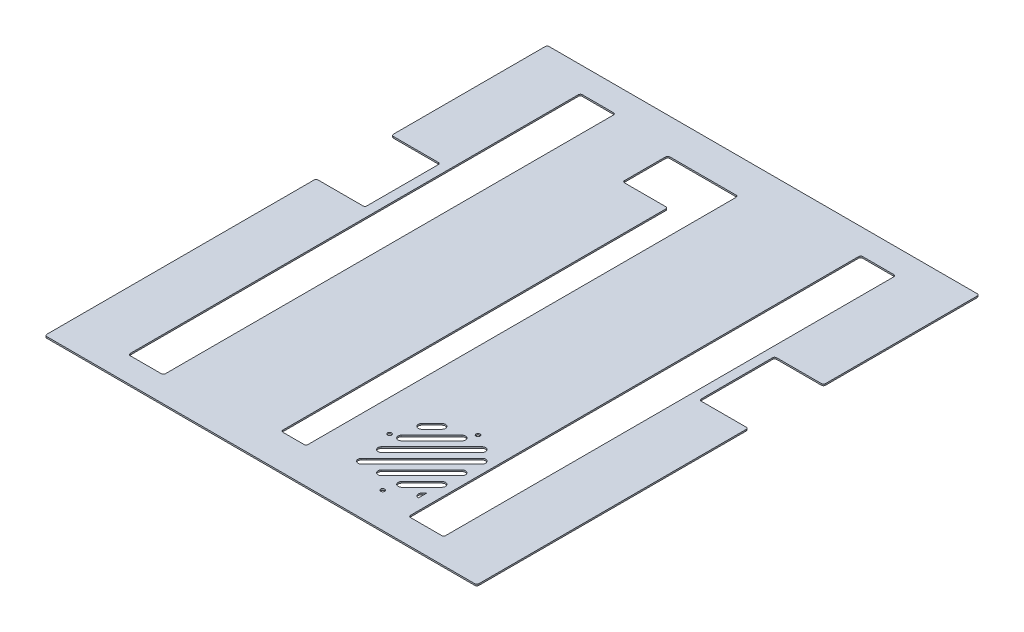
SolidWorks part; units mm, degrees
ref_plane "Front Plane" through (0, 0, 0) normal (0, 0, 1) x (1, 0, 0)
ref_plane "Top Plane" through (0, 0, 0) normal (0, 1, 0) x (1, 0, 0)
ref_plane "Right Plane" through (0, 0, 0) normal (1, 0, 0) x (0, 0, -1)
sketch "Sketch1" plane through (0, 0, 0) normal (0, 1, 0) x (1, 0, 0)
  line L1 (5911.0841, -8452.3124) -> (6341.0841, -8452.3124)
  line L2 (5911.0841, -8452.3124) -> (5911.0841, -8952.3124)
  line L3 (5911.0841, -8952.3124) -> (6341.0841, -8952.3124)
  line L4 (6341.0841, -8452.3124) -> (6341.0841, -8952.3124)
  dimension "D1" = 500
  dimension "D2" = 430
extrude "Boss-Extrude1" add sketch "Sketch1" along normal blind 1.5
sketch "Sketch2" plane through (0, 1.5, 0) normal (0, 1, 0) x (1, 0, 0)
  line L0 (5911.0841, -8452.3124) -> (5911.0841, -8952.3124) construction
  line L1 (5959.6841, -8682.3124) -> (5911.0841, -8682.3124)
  line L2 (5959.6841, -8682.3124) -> (5959.6841, -8607.3124)
  line L3 (5959.6841, -8607.3124) -> (5911.0841, -8607.3124)
  line L4 (5911.0841, -8682.3124) -> (5911.0841, -8607.3124)
  line L9 (6341.0841, -8952.3124) -> (6341.0841, -8452.3124) construction
  line L10 (6341.0841, -8682.3124) -> (6292.4841, -8682.3124)
  line L11 (6341.0841, -8682.3124) -> (6341.0841, -8607.3124)
  line L12 (6341.0841, -8607.3124) -> (6292.4841, -8607.3124)
  line L13 (6292.4841, -8682.3124) -> (6292.4841, -8607.3124)
  line L14 (6341.0841, -8452.3124) -> (5911.0841, -8452.3124) construction
  dimension "D1" = 48.6
  dimension "D2" = 75
  dimension "D3" = 75
  dimension "D4" = 48.6
  dimension "D5" = 155
extrude "Cut-Extrude1" cut sketch "Sketch2" against normal blind 10
sketch "Sketch3" plane through (0, 1.5, 0) normal (0, 1, 0) x (1, 0, 0)
  line L0 (5969.0841, -8541.6519) -> (5969.0841, -8927.3124)
  line L1 (6283.0841, -8927.3124) -> (6248.0841, -8927.3124)
  line L2 (6283.0841, -8927.3124) -> (6283.0841, -8477.3124)
  line L3 (6283.0841, -8477.3124) -> (6248.0841, -8477.3124)
  line L4 (6248.0841, -8927.3124) -> (6248.0841, -8477.3124)
  line L5 (5969.0841, -8477.3124) -> (6004.0841, -8477.3124)
  line L11 (5969.0841, -8927.3124) -> (6004.0841, -8927.3124)
  line L12 (6004.0841, -8477.3124) -> (6004.0841, -8927.3124)
  line L36 (5911.0841, -8682.3124) -> (5911.0841, -8952.3124) construction
  line L37 (6341.0841, -8952.3124) -> (6341.0841, -8682.3124) construction
  line L39 (6102.0841, -8487.3124) -> (6136.0841, -8487.3124)
  line L40 (6111.0841, -8532.3124) -> (6111.0841, -8917.3124)
  line L41 (6111.0841, -8917.3124) -> (6136.0841, -8917.3124)
  line L42 (6136.0841, -8487.3124) -> (6136.0841, -8917.3124)
  line L44 (6341.0841, -8452.3124) -> (5911.0841, -8452.3124) construction
  line L45 (5969.0841, -8477.3124) -> (5969.0841, -8541.6519)
  line L47 (5911.0841, -8952.3124) -> (6341.0841, -8952.3124) construction
  line L48 (6102.0841, -8487.3124) -> (6066.0841, -8487.3124)
  line L50 (6111.0841, -8532.3124) -> (6066.0841, -8532.3124)
  line L51 (6066.0841, -8487.3124) -> (6066.0841, -8532.3124)
  point P4 (6265.5841, -8477.3124)
  point P32 (6126.0841, -8452.3124)
  point P33 (6119.0841, -8487.3124)
  dimension "D15" = 35
  dimension "D22" = 45
  dimension "D1" = 35
  dimension "D3" = 35
  dimension "D4" = 25
  dimension "D5" = 25
  dimension "D6" = 58
  dimension "D7" = 45
  dimension "D8" = 58
  dimension "D9" = 205
  dimension "D10" = 35
  dimension "D11" = 200
  dimension "D20" = 25
  dimension "D21" = 25
extrude "Cut-Extrude2" cut sketch "Sketch3" against normal blind 10
sketch "Sketch4" plane through (0, 1.5, 0) normal (0, 1, 0) x (1, 0, 0)
  line L0 (6237.0841, -8848.0965) -> (6237.0841, -8858.0965) construction
  line L1 (6237.0841, -8898.0965) -> (6207.0841, -8898.0965) construction
  line L3 (6237.0841, -8833.0965) -> (6192.0841, -8833.0965) construction
  line L4 (6177.0841, -8898.0965) -> (6177.0841, -8848.0965) construction
  line L5 (5911.0841, -8952.3124) -> (6341.0841, -8952.3124) construction
  line L6 (6177.0841, -8898.0965) -> (6234.5841, -8840.5965)
  line L7 (6179.5841, -8885.5965) -> (6229.5841, -8835.5965)
  line L8 (6174.5841, -8880.5965) -> (6222.0841, -8833.0965)
  line L9 (6177.0841, -8898.0965) -> (6174.5841, -8900.5965)
  line L10 (6174.5841, -8880.5965) -> (6222.0841, -8833.0965)
  line L11 (6179.5841, -8865.5965) -> (6209.5841, -8835.5965)
  line L12 (6177.0841, -8898.0965) -> (6174.5841, -8900.5965) construction
  line L13 (6179.5841, -8865.5965) -> (6209.5841, -8835.5965)
  line L14 (6174.5841, -8860.5965) -> (6204.5841, -8830.5965)
  line L15 (6237.0841, -8888.0965) -> (6239.5841, -8885.5965)
  line L16 (6174.5841, -8860.5965) -> (6204.5841, -8830.5965)
  line L17 (6179.5841, -8845.5965) -> (6189.5841, -8835.5965)
  line L18 (6174.5841, -8840.5965) -> (6184.5841, -8830.5965)
  line L19 (6179.5841, -8885.5965) -> (6229.5841, -8835.5965)
  line L20 (6177.0841, -8878.0965) -> (6222.0841, -8833.0965)
  line L21 (6179.5841, -8865.5965) -> (6209.5841, -8835.5965)
  line L22 (6187.0841, -8898.0965) -> (6237.0841, -8848.0965)
  line L23 (6197.0841, -8898.0965) -> (6234.5841, -8860.5965)
  line L24 (6207.0841, -8898.0965) -> (6237.0841, -8868.0965)
  line L25 (6194.5841, -8900.5965) -> (6234.5841, -8860.5965)
  line L26 (6199.5841, -8905.5965) -> (6237.0841, -8868.0965)
  line L27 (6214.5841, -8900.5965) -> (6234.5841, -8880.5965)
  line L28 (6199.5841, -8905.5965) -> (6237.0841, -8868.0965)
  line L29 (6214.5841, -8900.5965) -> (6234.5841, -8880.5965)
  line L30 (6219.5841, -8905.5965) -> (6237.0841, -8888.0965)
  line L31 (6214.5841, -8900.5965) -> (6234.5841, -8880.5965)
  line L32 (6219.5841, -8905.5965) -> (6237.0841, -8888.0965)
  line L33 (6234.5841, -8900.5965) -> (6237.0841, -8898.0965)
  line L34 (6179.5841, -8905.5965) -> (6237.0841, -8848.0965)
  line L35 (6194.5841, -8900.5965) -> (6234.5841, -8860.5965)
  line L36 (6199.5841, -8905.5965) -> (6237.0841, -8868.0965)
  line L37 (6182.0841, -8833.0965) -> (6192.0841, -8833.0965) construction
  line L38 (6182.0841, -8833.0965) -> (6177.0841, -8833.0965) construction
  line L39 (6177.0841, -8863.0965) -> (6237.0841, -8863.0965) construction
  line L40 (6177.0841, -8838.0965) -> (6177.0841, -8833.0965) construction
  line L41 (6177.0841, -8838.0965) -> (6177.0841, -8848.0965) construction
  line L42 (6197.0841, -8898.0965) -> (6177.0841, -8898.0965) construction
  line L43 (6179.5841, -8865.5965) -> (6209.5841, -8835.5965)
  line L44 (6174.5841, -8860.5965) -> (6204.5841, -8830.5965)
  line L45 (6179.5841, -8845.5965) -> (6189.5841, -8835.5965)
  line L46 (6147.0841, -8878.0965) -> (6157.0841, -8868.0965) [skipped]
  line L47 (6147.0841, -8898.0965) -> (6157.0841, -8888.0965) [skipped]
  line L48 (6147.0841, -8888.0965) -> (6157.0841, -8878.0965) [skipped]
  line L49 (6237.0841, -8868.0965) -> (6239.5841, -8865.5965)
  line L52 (6222.0841, -8833.0965) -> (6224.5841, -8830.5965)
  line L54 (6237.0841, -8833.0965) -> (6237.0841, -8839.561) construction
  line L55 (6237.0841, -8898.0965) -> (6237.0841, -8906.6321)
  line L57 (6237.0841, -8888.0965) -> (6237.0841, -8898.0965) construction
  line L59 (6237.0841, -8848.0965) -> (6239.5841, -8845.5965)
  line L60 (6237.0841, -8868.0965) -> (6237.0841, -8879.561) construction
  arc A1 (6189.5841, -8835.5965) -> (6184.5841, -8830.5965) centre (6187.0841, -8833.0965) ccw
  arc A2 (6209.5841, -8835.5965) -> (6204.5841, -8830.5965) centre (6207.0841, -8833.0965) ccw
  arc A3 (6229.5841, -8835.5965) -> (6224.5841, -8830.5965) centre (6227.0841, -8833.0965) ccw
  arc A5 (6174.5841, -8840.5965) -> (6179.5841, -8845.5965) centre (6177.0841, -8843.0965) ccw
  arc A6 (6174.5841, -8860.5965) -> (6179.5841, -8865.5965) centre (6177.0841, -8863.0965) ccw
  arc A7 (6174.5841, -8880.5965) -> (6179.5841, -8885.5965) centre (6177.0841, -8883.0965) ccw
  arc A8 (6174.5841, -8900.5965) -> (6179.5841, -8905.5965) centre (6177.0841, -8903.0965) ccw
  arc A9 (6194.5841, -8900.5965) -> (6199.5841, -8905.5965) centre (6197.0841, -8903.0965) ccw
  arc A10 (6214.5841, -8900.5965) -> (6219.5841, -8905.5965) centre (6217.0841, -8903.0965) ccw
  arc A11 (6234.5841, -8900.5965) -> (6237.0841, -8906.6321) centre (6237.0841, -8903.0965) ccw
  arc A12 (6249.5841, -8835.5965) -> (6244.5841, -8830.5965) centre (6247.0841, -8833.0965) ccw [skipped]
  arc A13 (6239.5841, -8845.5965) -> (6234.5841, -8840.5965) centre (6237.0841, -8843.0965) ccw
  arc A14 (6239.5841, -8865.5965) -> (6234.5841, -8860.5965) centre (6237.0841, -8863.0965) ccw
  arc A15 (6239.5841, -8885.5965) -> (6234.5841, -8880.5965) centre (6237.0841, -8883.0965) ccw
  dimension "D8" = 4
  dimension "D1" = 65
  dimension "D3" = 54.2159
  dimension "D4" = 4
  dimension "D5" = 4
  dimension "D6" = 4
  dimension "D7" = 4
  dimension "D9" = 4
  dimension "D10" = 4
extrude "Cut-Extrude3" cut sketch "Sketch4" against normal blind 10
fillet "Fillet2" radius 2 12 edges at (6292.4841, 0.75, 8607.3124) (6341.0841, 0.75, 8607.3124) (6341.0841, 0.75, 8682.3124) (6292.4841, 0.75, 8682.3124) (5959.6841, 0.75, 8607.3124) (5959.6841, 0.75, 8682.3124) (5911.0841, 0.75, 8682.3124) (5911.0841, 0.75, 8607.3124) (5911.0841, 0.75, 8452.3124) (6341.0841, 0.75, 8452.3124) (6341.0841, 0.75, 8952.3124) (5911.0841, 0.75, 8952.3124)
fillet "Fillet3" radius 2 14 edges at (6004.0841, 0.75, 8927.3124) (5969.0841, 0.75, 8927.3124) (6004.0841, 0.75, 8477.3124) (5969.0841, 0.75, 8477.3124) (6283.0841, 0.75, 8927.3124) (6248.0841, 0.75, 8927.3124) (6283.0841, 0.75, 8477.3124) (6248.0841, 0.75, 8477.3124) (6136.0841, 0.75, 8917.3124) (6111.0841, 0.75, 8917.3124) (6136.0841, 0.75, 8487.3124) (6111.0841, 0.75, 8532.3124) (6066.0841, 0.75, 8487.3124) (6066.0841, 0.75, 8532.3124)
sketch "Sketch6" plane through (0, 1.5, 0) normal (0, 1, 0) x (1, 0, 0)
  line L0 (6177.0841, -8833.0965) -> (6248.0841, -8833.0965) construction
  line L1 (6248.0841, -8479.3124) -> (6248.0841, -8925.3124) construction
  line L2 (6248.0841, -8833.0965) -> (6248.0841, -8898.0738) construction
  line L3 (6248.0841, -8898.0738) -> (6177.0841, -8898.0965) construction
  line L4 (6177.0841, -8898.0965) -> (6177.0841, -8833.0965) construction
  line L5 (6177.0841, -8865.5965) -> (6248.0841, -8865.5852) construction
  line L6 (6212.5841, -8833.0965) -> (6212.5841, -8898.0852) construction
  line L7 (6212.5841, -8833.0965) -> (6212.5841, -8822.5908) construction
  line L8 (6177.0841, -8865.5965) -> (6167.5841, -8865.5965) construction
  line L9 (6212.5841, -8898.0852) -> (6212.5841, -8917.5908) construction
  line L10 (6237.0841, -8833.0965) -> (6237.0841, -8839.561) construction
  circle A0 centre (6212.5841, -8822.5908) radius 2
  circle A1 centre (6212.5841, -8917.5908) radius 2
  circle A2 centre (6167.5841, -8865.5965) radius 2
  dimension "D1" = 4
  dimension "D2" = 4
  dimension "D3" = 4
  dimension "D4" = 95
  dimension "D5" = 43
  dimension "D6" = 45
  dimension "D7" = 24.5
extrude "Cut-Extrude4" cut sketch "Sketch6" against normal blind 10
